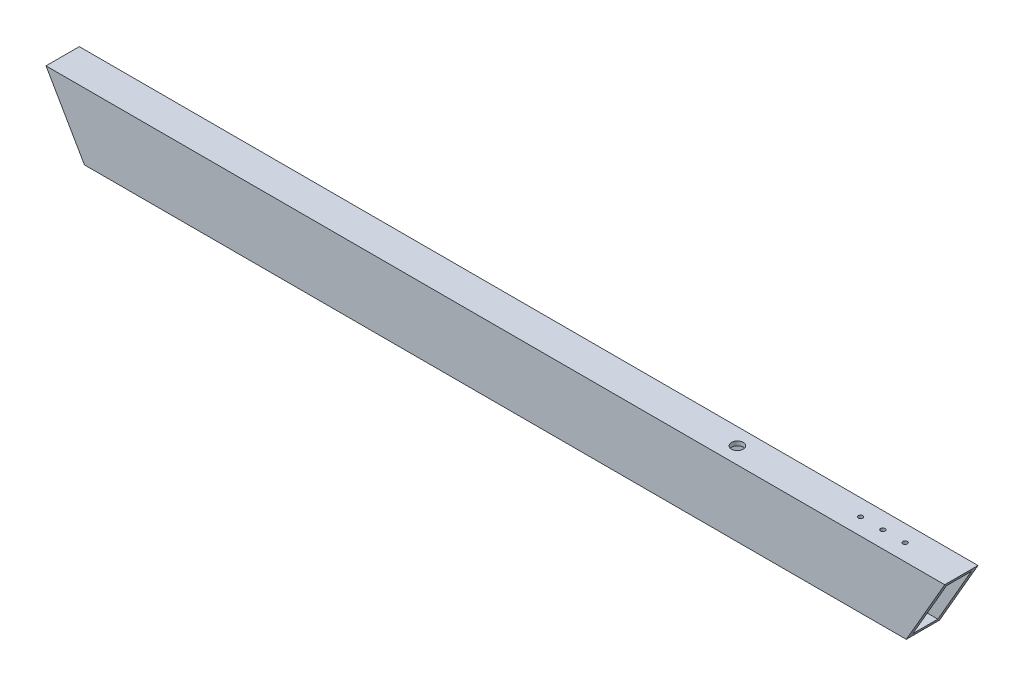
SolidWorks part; units mm, degrees
ref_plane "Front Plane" through (0, 0, 0) normal (0, 0, 1) x (1, 0, 0)
ref_plane "Top Plane" through (0, 0, 0) normal (0, 1, 0) x (1, 0, 0)
ref_plane "Right Plane" through (0, 0, 0) normal (1, 0, 0) x (0, 0, -1)
sketch "Sketch1" plane through (0, 0, 0) normal (1, 0, 0) x (0, 0, -1)
  line L1 (-9.525, -22.225) -> (9.525, -22.225)
  line L2 (-9.525, -22.225) -> (-9.525, 22.225)
  line L3 (-9.525, 22.225) -> (9.525, 22.225)
  line L4 (9.525, -22.225) -> (9.525, 22.225)
  line L5 (-9.525, -22.225) -> (9.525, 22.225) construction
  line L6 (-9.525, 22.225) -> (9.525, -22.225) construction
  line L7 (-12.7, -25.4) -> (12.7, -25.4)
  line L8 (-12.7, -25.4) -> (-12.7, 25.4)
  line L9 (-12.7, 25.4) -> (12.7, 25.4)
  line L10 (12.7, -25.4) -> (12.7, 25.4)
  line L11 (-12.7, -25.4) -> (12.7, 25.4) construction
  line L12 (-12.7, 25.4) -> (12.7, -25.4) construction
  point P0 (0, 0)
  point P6 (0, 0)
  dimension "D1" = 25.4
  dimension "D2" = 50.8
  dimension "D3" = 3.175
  dimension "D4" = 3.175
extrude "Boss-Extrude1" add sketch "Sketch1" along normal mid plane 685.8
sketch "Sketch2" plane through (0, 0, -12.7) normal (0, 0, -1) x (-1, 0, 0)
  line L0 (342.9, 25.4) -> (313.5706, -25.4)
  line L1 (-342.9, -25.4) -> (342.9, -25.4) construction
  line L3 (0, 13.97) -> (0, -13.97) construction
  line L4 (-342.9, 25.4) -> (-313.5706, -25.4)
  line M2 (342.9, -25.4) -> (342.9, 25.4)
  line M4 (-342.9, 25.4) -> (-342.9, -25.4)
  line M5 (-342.9, -25.4) -> (342.9, -25.4)
  dimension "D1" = 60
extrude "Cut-Extrude1" cut sketch "Sketch2" against normal through all and the other way through all contours L0 M2 M5 | L4 M4 M5
sketch "Sketch3" plane through (0, 0, -12.7) normal (0, 0, -1) x (-1, 0, 0)
  line L0 (-313.5706, -25.4) -> (313.5706, -25.4) construction
  circle A0 centre (-234.95, 0) radius 11.1125
  circle A1 centre (-190.5, 0) radius 11.1125
  dimension "D1" = 22.225
  dimension "D4" = 107.95
  dimension "D5" = 44.45
  dimension "D2" = 25.4
  dimension "D3" = 2
extrude "Cut-Extrude2" cut sketch "Sketch3" against normal up to next
hole_wizard "M3 Clearance Hole1" positions "Sketch5" profile "Sketch6" hole size "M3" standard "ANSI Metric" end condition up to next
sketch "Sketch5" plane through (0, 25.4, 0) normal (0, 1, 0) x (1, 0, 0)
  point P0 (299.9914, 0)
  point P3 (282.9914, 0)
  point P13 (265.9914, 0)
sketch "Sketch6" plane through (299.9914, 25.4, 0) normal (1, 0, 0) x (0, 0, 1)
  line L0 (0, 0) -> (0, 3.175)
  line L1 (0, 3.175) -> (1.7, 3.175)
  line L2 (1.7, 3.175) -> (1.7, 0)
  line L5 (1.7, 0) -> (0, 0)
  line L11 (0, -6.35) -> (0, 107.95) construction
  dimension "Thru Hole Dia." = 3.4
  dimension "Thru Hole Depth" = 3.175
sketch "Sketch9" plane through (0, 25.4, 0) normal (0, 1, 0) x (1, 0, 0)
  circle A0 centre (171.9914, 0) radius 4.5
  dimension "D1" = 9
extrude "Cut-Extrude3" cut sketch "Sketch9" against normal blind 12.7 contours A0
